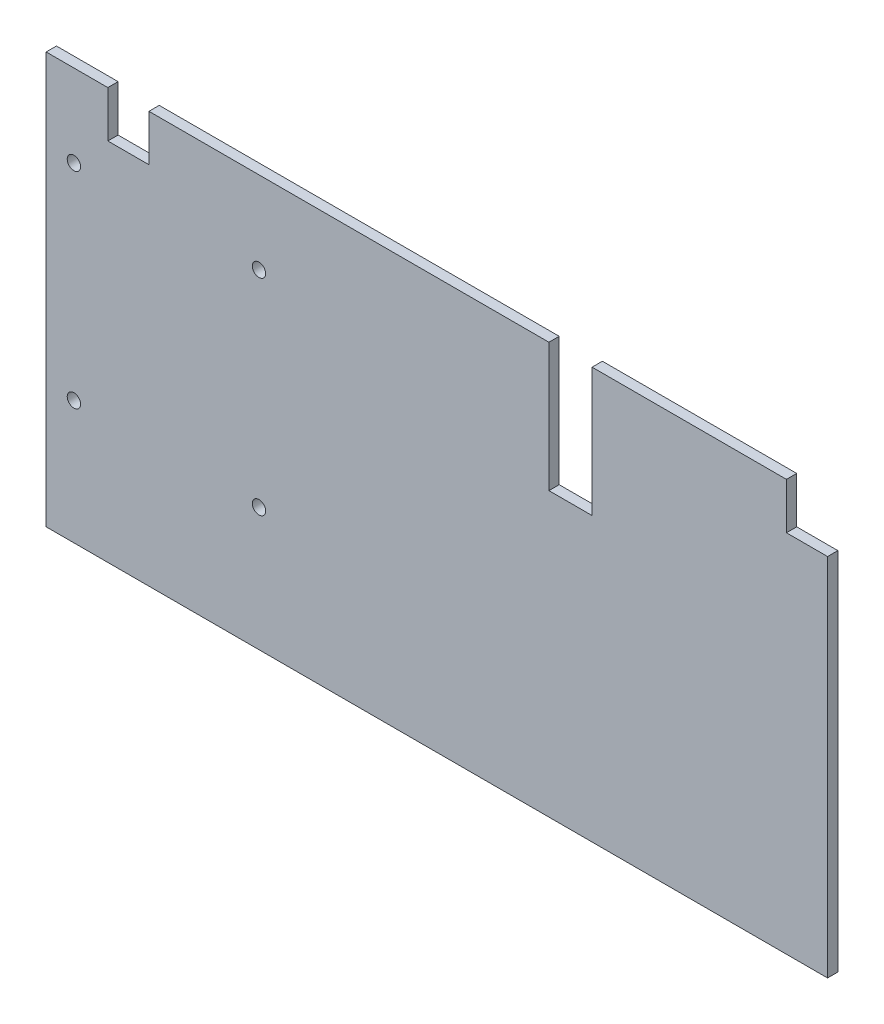
SolidWorks part; units mm, degrees
material "1.0545 (S355N)"
ref_plane "Front Plane" through (0, 0, 0) normal (0, 0, 1) x (1, 0, 0)
ref_plane "Top Plane" through (0, 0, 0) normal (0, 1, 0) x (1, 0, 0)
ref_plane "Right Plane" through (0, 0, 0) normal (1, 0, 0) x (0, 0, -1)
sketch "Sketch1" plane through (0, 0, 0) normal (0, 0, 1) x (1, 0, 0)
  line L0 (0, 460.58) -> (0, -350.58) construction
  line L5 (-393, 300.7391) -> (-393, -210.0403) construction
  line L6 (-21, 55) -> (21, 55)
  line L7 (0, 0) -> (-447.8579, 0) construction
  line L8 (-21, 55) -> (-21, 180)
  line L9 (-21, 180) -> (-410, 180)
  line L10 (21, 55) -> (21, 180)
  line L11 (21, 180) -> (210, 180)
  line L12 (210, 180) -> (210, 135)
  line L13 (210, 135) -> (250, 135)
  line L14 (250, 135) -> (250, -220)
  line L15 (-410, 180) -> (-410, 135)
  line L16 (-410, 135) -> (-450, 135)
  line L17 (-510, 180) -> (-510, -220)
  line L18 (-510, -220) -> (250, -220)
  line L19 (-450, 135) -> (-450, 180)
  line L20 (-450, 180) -> (-510, 180)
  circle A0 centre (-303, 100) radius 6.5
  circle A1 centre (-483, 100) radius 6.5
  circle A2 centre (-303, -100) radius 6.5
  circle A3 centre (-483, -100) radius 6.5
  point P7 (0, 55)
  dimension "D12" = 13
  dimension "D13" = 400
  dimension "D1" = 393
  dimension "D2" = 42
  dimension "D3" = 55
  dimension "D4" = 125
  dimension "D5" = 40
  dimension "D6" = 45
  dimension "D7" = 189
  dimension "D8" = 660
  dimension "D9" = 45
  dimension "D10" = 90
  dimension "D11" = 100
  dimension "D14" = 40
  dimension "D15" = 760
extrude "Boss-Extrude1" add sketch "Sketch1" along normal blind 10
